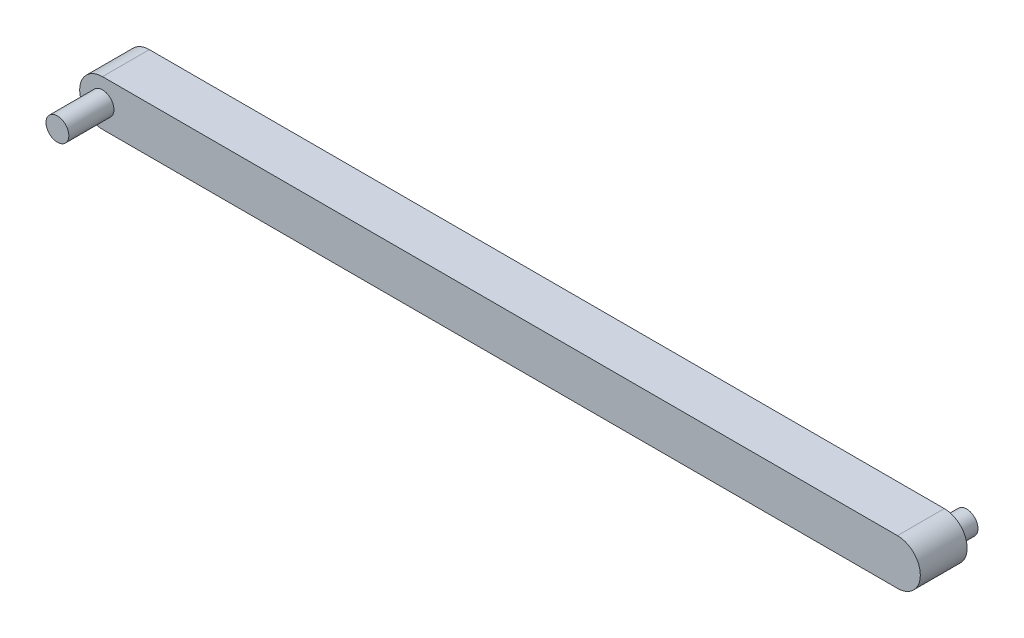
SolidWorks part; units mm, degrees
ref_plane "Plan de face" through (0, 0, 0) normal (0, 0, 1) x (1, 0, 0)
ref_plane "Plan de dessus" through (0, 0, 0) normal (0, 1, 0) x (1, 0, 0)
ref_plane "Plan de droite" through (0, 0, 0) normal (1, 0, 0) x (0, 0, -1)
sketch "Esquisse1" plane through (0, 0, 0) normal (0, 0, 1) x (1, 0, 0)
  line L1 (-28.7902, 6.6031) -> (145.2098, 6.6031)
  line L3 (-28.7902, -3.3969) -> (145.2098, -3.3969)
  arc A0 (-28.7902, 6.6031) -> (-28.7902, -3.3969) centre (-28.7902, 1.6031) ccw
  arc A1 (145.2098, -3.3969) -> (145.2098, 6.6031) centre (145.2098, 1.6031) ccw
  dimension "D2" = 10
  dimension "D3" = 10
  dimension "D1" = 10
extrude "Boss.-Extru.1" add sketch "Esquisse1" along normal mid plane 10.25
sketch "Esquisse2" plane through (0, 0, 0) normal (0, 0, 1) x (1, 0, 0)
  circle A0 centre (-28.7902, 1.6031) radius 2.5
  dimension "D1" = 5
extrude "Boss.-Extru.2" add sketch "Esquisse2" along normal blind 15
sketch "Esquisse3" plane through (0, 0, 0) normal (0, 0, 1) x (1, 0, 0)
  circle A0 centre (145.2098, 1.6031) radius 2.5
  dimension "D1" = 5
extrude "Boss.-Extru.3" add sketch "Esquisse3" against normal blind 10
